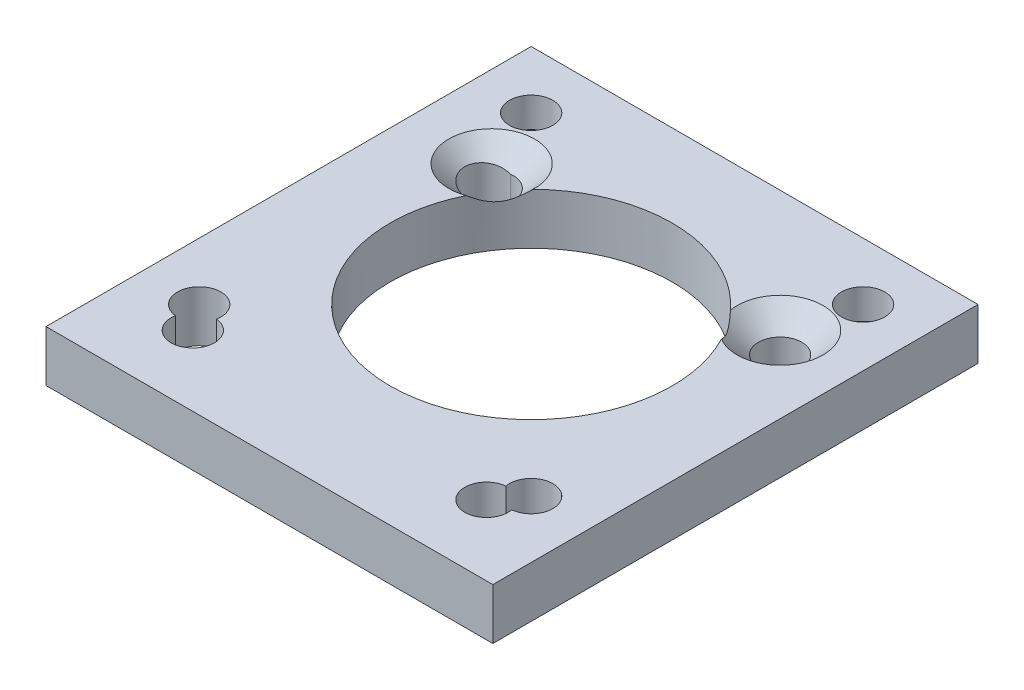
SolidWorks part; units mm, degrees
ref_plane "Front Plane" through (0, 0, 0) normal (0, 0, 1) x (1, 0, 0)
ref_plane "Top Plane" through (0, 0, 0) normal (0, 1, 0) x (1, 0, 0)
ref_plane "Right Plane" through (0, 0, 0) normal (1, 0, 0) x (0, 0, -1)
sketch "Sketch1" plane through (0, 0, 0) normal (0, 1, 0) x (1, 0, 0)
  line L1 (-17.5, -19) -> (17.5, -19)
  line L2 (-17.5, -19) -> (-17.5, 19)
  line L3 (-17.5, 19) -> (17.5, 19)
  line L4 (17.5, -19) -> (17.5, 19)
  line L5 (-17.5, -19) -> (17.5, 19) construction
  line L6 (-17.5, 19) -> (17.5, -19) construction
  point P0 (0, 0)
  dimension "D1" = 38
  dimension "D2" = 35
extrude "Boss-Extrude1" add sketch "Sketch1" along normal blind 4
hole_wizard "M3 Clearance Hole1" positions "Sketch2" profile "Sketch3" hole size "M3" standard "ISO" end condition through all
sketch "Sketch2" plane through (0, 0, 0) normal (0, -1, 0) x (-1, 0, 0)
  point P0 (-11.5, -13.5)
  point P3 (-11.5, 9.5)
  point P6 (11.5, 9.5)
  point P9 (11.5, -13.5)
sketch "Sketch3" plane through (11.5, 0, 13.5) normal (1, 0, 0) x (0, 0, -1)
  line L0 (0, 0) -> (0, 4)
  line L1 (0, 4) -> (1.7, 4)
  line L2 (1.7, 4) -> (1.7, 0)
  line L5 (1.7, 0) -> (0, 0)
  line L11 (0, -6.35) -> (0, 107.95) construction
  dimension "Thru Hole Dia." = 3.4
  dimension "Thru Hole Depth" = 4
sketch "Sketch4" plane through (0, 4, 0) normal (0, 1, 0) x (1, 0, 0)
  circle A0 centre (0, 1.5) radius 11.05
  circle A1 centre (0, 1.5) radius 11 construction
  point P3 (0, 0)
  point P4 (-0.435, 1.218)
  dimension "D1" = 22.1
extrude "Cut-Extrude1" cut sketch "Sketch4" against normal through all
hole_wizard "M3 Clearance Hole2" positions "Sketch5" profile "Sketch6" hole size "M3" standard "ISO" end condition through all
sketch "Sketch5" plane through (0, 4, 0) normal (0, 1, 0) x (1, 0, 0)
  point P0 (-13, 14.5)
  point P3 (13, 14.5)
  point P7 (-13, -11.5)
  point P10 (13, -11.5)
sketch "Sketch6" plane through (-13, 4, -14.5) normal (1, 0, 0) x (0, 0, 1)
  line L0 (0, 0) -> (0, 4)
  line L1 (0, 4) -> (1.7, 4)
  line L2 (1.7, 4) -> (1.7, 0)
  line L5 (1.7, 0) -> (0, 0)
  line L11 (0, -6.35) -> (0, 107.95) construction
  dimension "Thru Hole Dia." = 3.4
  dimension "Thru Hole Depth" = 4
hole_wizard "CSK for M3 Hex Socket Countersunk Cap Screw1" positions "Sketch7" profile "Sketch8" countersink size "M3" standard "ISO" end condition through all
sketch "Sketch7" plane through (0, 0, 0) normal (0, -1, 0) x (-1, 0, 0)
  point P6 (-13, 14.5)
  point P9 (13, 14.5)
  point P13 (0, 0)
  point P14 (0, 0)
sketch "Sketch8" plane through (13, 0, -14.5) normal (1, 0, 0) x (0, 0, -1)
  line L0 (0, 0) -> (0, 4)
  line L1 (0, 4) -> (1.7, 4)
  line L2 (1.7, 4) -> (1.7, 1.66)
  line L3 (1.7, 1.66) -> (3.36, 0)
  line L5 (3.36, 0) -> (0, 0)
  line L6 (-1.7, 1.66) -> (-3.36, 0) construction
  line L11 (0, -6.35) -> (0, 107.95) construction
  dimension "Thru Hole Dia." = 3.4
  dimension "Thru Hole Depth" = 4
  dimension "Near C'Sink Dia." = 6.72
  dimension "Near C'Sink Angle" = 90
hole_wizard "CSK for M3 Hex Socket Countersunk Cap Screw2" positions "Sketch9" profile "Sketch10" countersink size "M3" standard "ISO" end condition through all
sketch "Sketch9" plane through (0, 4, 0) normal (0, 1, 0) x (1, 0, 0)
  point P0 (11.5, 9.5)
  point P3 (-11.0932, 9.5)
sketch "Sketch10" plane through (11.5, 4, -9.5) normal (1, 0, 0) x (0, 0, 1)
  line L0 (0, 0) -> (0, 4)
  line L1 (0, 4) -> (1.7, 4)
  line L2 (1.7, 4) -> (1.7, 1.66)
  line L3 (1.7, 1.66) -> (3.36, 0)
  line L5 (3.36, 0) -> (0, 0)
  line L6 (-1.7, 1.66) -> (-3.36, 0) construction
  line L11 (0, -6.35) -> (0, 107.95) construction
  dimension "Thru Hole Dia." = 3.4
  dimension "Thru Hole Depth" = 4
  dimension "Near C'Sink Dia." = 6.72
  dimension "Near C'Sink Angle" = 90
